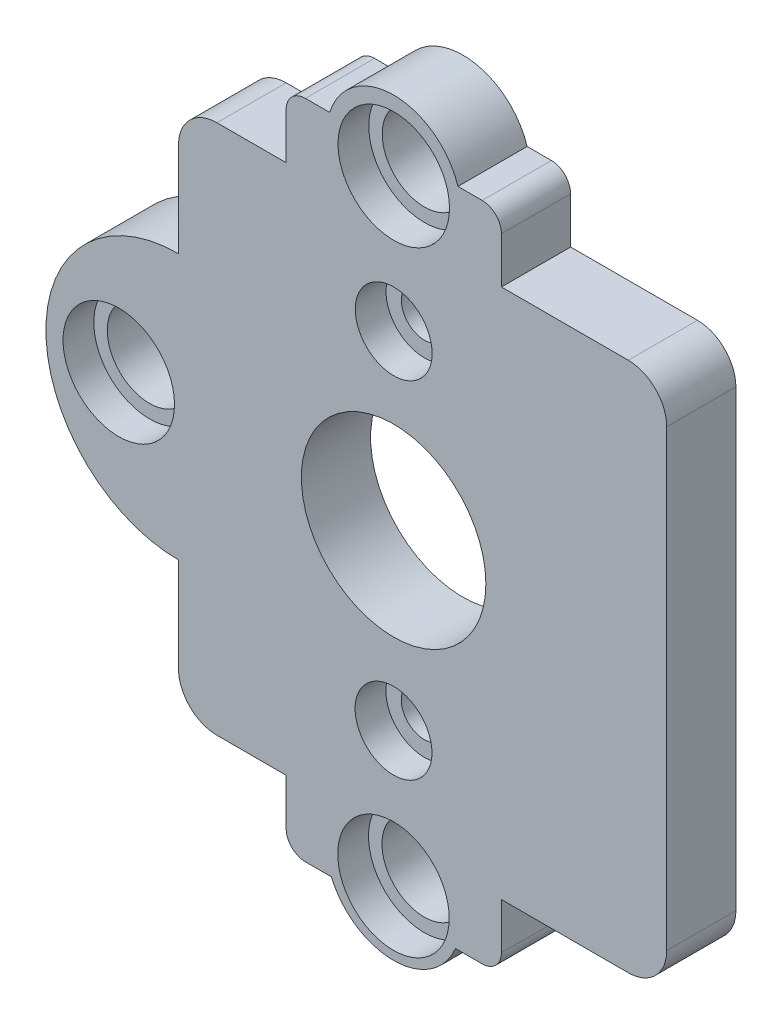
SolidWorks part; units mm, degrees
ref_plane "Ebene vorne" through (0, 0, 0) normal (0, 0, 1) x (1, 0, 0)
ref_plane "Ebene oben" through (0, 0, 0) normal (0, 1, 0) x (1, 0, 0)
ref_plane "Ebene rechts" through (0, 0, 0) normal (1, 0, 0) x (0, 0, -1)
sketch "body" plane through (0, 0, 0) normal (0, 0, 1) x (1, 0, 0)
  line L0 (0, 10.355) -> (0, -9.4721) construction
  line L1 (0, 16.1937) -> (-2.8, 16.1937)
  line L2 (-2.8, 16.1937) -> (-2.8, 14.4937)
  line L3 (-2.8, 14.4937) -> (-5.6, 14.4937)
  line L4 (-5.6, 14.4937) -> (-5.6, 0.6937)
  line L5 (-5.6, 0.6937) -> (-2.8, 0.6937)
  line L6 (-2.8, 0.6937) -> (-2.8, -1.0063)
  line L7 (-2.8, -1.0063) -> (0, -1.0063)
  line L8 (0, -1.0063) -> (2.8, -1.0063)
  line L9 (2.8, -1.0063) -> (2.8, 0.6937)
  line L10 (2.8, 0.6937) -> (5.6, 0.6937)
  line L11 (5.6, 0.6937) -> (5.6, 14.4937)
  line L12 (5.6, 14.4937) -> (2.8, 14.4937)
  line L13 (2.8, 14.4937) -> (2.8, 16.1937)
  line L14 (2.8, 16.1937) -> (0, 16.1937)
  line L15 (0, 16.1937) -> (0, -1.0063) construction
  dimension "D1" = 5.6
  dimension "D2" = 17.2
  dimension "D3" = 2.8
  dimension "D4" = 13.8
extrude "body_" add sketch "body" along normal mid plane 1.8
sketch "side_extender" plane through (0, 0, 0.9) normal (0, 0, 1) x (1, 0, 0)
  line L0 (0, -1.0063) -> (0, 16.1937) construction
  line L2 (-2.8, -1.0063) -> (2.8, -1.0063) construction
  line L3 (2.8, 16.1937) -> (-2.8, 16.1937) construction
  circle A0 centre (0, 15.668) radius 1.75
  circle A1 centre (-0.0089, -0.332) radius 1.75
  point P14 (-0.145, 7.5182)
  dimension "D1" = 16
  dimension "D2" = 3.5
extrude "side-extender" add sketch "side_extender" against normal blind 1.8
sketch "center-extern" plane through (0, 0, 0.9) normal (0, 0, 1) x (1, 0, 0)
  line L0 (-5.6, 7.5937) -> (5.6, 7.5937) construction
  line L1 (-5.6, 14.4937) -> (-5.6, 0.6937) construction
  line L2 (5.6, 0.6937) -> (5.6, 14.4937) construction
  line L3 (-5.6, 11.0437) -> (-5.6, 4.1437)
  line L4 (4.1, 14.4937) -> (7.1, 14.4937)
  line L5 (4.1, 14.4937) -> (4.1, 0.6937)
  line L6 (4.1, 0.6937) -> (7.1, 0.6937)
  line L7 (7.1, 14.4937) -> (7.1, 0.6937)
  line L8 (4.1, 14.4937) -> (7.1, 0.6937) construction
  line L9 (4.1, 0.6937) -> (7.1, 14.4937) construction
  arc A0 (-5.6, 11.0437) -> (-5.6, 4.1437) centre (-5.6, 7.5937) ccw
  dimension "D3" = 3.45
  dimension "D1" = 13.8
  dimension "D2" = 3
extrude "Extender-center" add sketch "center-extern" against normal blind 1.8
sketch "holes" plane through (0, 0, 0.9) normal (0, 0, 1) x (1, 0, 0)
  line L0 (0, 17.418) -> (-0.0089, -2.082) construction
  line L1 (-9.05, 7.5937) -> (7.1, 7.5937) construction
  line L2 (7.1, 0.6937) -> (7.1, 14.4937) construction
  arc A0 (1.6692, 16.1937) -> (-1.6692, 16.1937) centre (0, 15.668) ccw construction
  arc A1 (-1.6238, -1.0063) -> (1.606, -1.0063) centre (-0.0089, -0.332) ccw construction
  arc A2 (-5.6, 11.0437) -> (-5.6, 4.1437) centre (-5.6, 7.5937) ccw construction
  circle A3 centre (-7.1545, 7.5937) radius 1.1
  circle A4 centre (-0.0008, 15.5937) radius 1.1
  circle A5 centre (-0.0082, -0.4063) radius 1.1
  circle A6 centre (-0.0024, 12.0937) radius 0.6
  circle A7 centre (-0.0066, 3.0937) radius 0.6
  dimension "D2" = 2.2
  dimension "D3" = 2.2
  dimension "D4" = 8
  dimension "D6" = 1.2
  dimension "7.15" = 7.15
  dimension "D5" = 8
  dimension "D7" = 4.5
  dimension "D8" = 4.5
extrude "screw-holes" cut sketch "holes" against normal blind 1.8
sketch "shaft hole" plane through (0, 0, 0.9) normal (0, 0, 1) x (1, 0, 0)
  line L0 (0, 17.2894) -> (-0.0089, -2.082) construction
  arc A0 (-1.6238, -1.0063) -> (1.606, -1.0063) centre (-0.0089, -0.332) ccw construction
  circle A1 centre (-0.0045, 7.6037) radius 2.4
  dimension "D1" = 4.8
extrude "motor shaft" cut sketch "shaft hole" against normal blind 1.8
sketch "Skizze6" plane through (0, 0, 0.9) normal (0, 0, 1) x (1, 0, 0)
  circle A0 centre (-0.0024, 12.0937) radius 1
  circle A1 centre (-0.0066, 3.0937) radius 1
  circle A2 centre (-0.0008, 15.5937) radius 1.45
  circle A3 centre (-0.0082, -0.4063) radius 1.45
  circle A4 centre (-7.1545, 7.5937) radius 1.45
  dimension "D1" = 2
  dimension "D2" = 2.9
extrude "Schnitt-Linear austragen5" cut sketch "Skizze6" against normal blind 0.8
fillet "Verrundung1" radius 1 4 edges at (-5.6, 0.6937, 0) (-5.6, 14.4937, 0) (7.1, 0.6937, 0) (7.1, 14.4937, 0)
fillet "Verrundung2" radius 0.5 4 edges at (-2.8, 16.1937, 0) (2.8, 16.1937, 0) (2.8, -1.0063, 0) (-2.8, -1.0063, 0)
